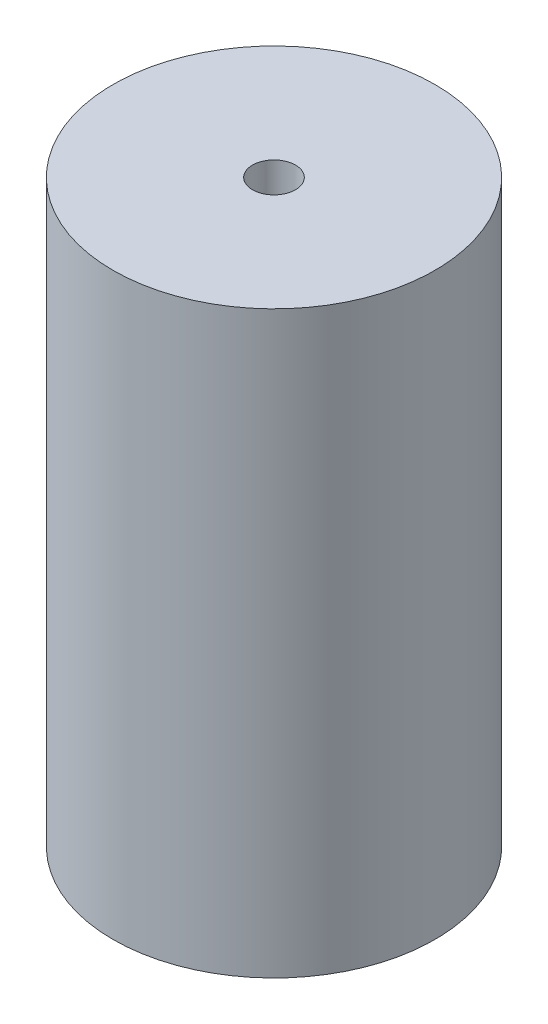
SolidWorks part; units mm, degrees
ref_plane "Front Plane" through (0, 0, 0) normal (0, 0, 1) x (1, 0, 0)
ref_plane "Top Plane" through (0, 0, 0) normal (0, 1, 0) x (1, 0, 0)
ref_plane "Right Plane" through (0, 0, 0) normal (1, 0, 0) x (0, 0, -1)
sketch "Sketch1" plane through (0, 0, 0) normal (0, 1, 0) x (1, 0, 0)
  circle A0 centre (0, 0) radius 7.5
  dimension "D1" = 15
extrude "Boss-Extrude1" add sketch "Sketch1" along normal blind 27
sketch "Sketch2" plane through (0, 0, 0) normal (0, -1, 0) x (1, 0, 0)
  circle A0 centre (0, 0) radius 5
  dimension "D1" = 10
extrude "Cut-Extrude1" cut sketch "Sketch2" against normal blind 11
sketch "Sketch3" plane through (0, 27, 0) normal (0, 1, 0) x (1, 0, 0)
  circle A0 centre (0, 0) radius 1
  dimension "D1" = 2
extrude "Cut-Extrude2" cut sketch "Sketch3" against normal blind 11
sketch "Sketch4" plane through (0, 0, 0) normal (0, 0, 1) x (1, 0, 0)
  line L0 (-7.5, 0) -> (7.5, 0) construction
  line L1 (7.5, 27) -> (-7.5, 27) construction
  circle A0 centre (0, 22) radius 1.6
  circle A1 centre (0, 5) radius 1.6
  dimension "D1" = 3.2
  dimension "D2" = 3.2
  dimension "D3" = 5
  dimension "D4" = 5
extrude "Cut-Extrude3" cut sketch "Sketch4" against normal blind 11
chamfer "Chamfer1" distance 1 angle 60 1 edges at (0, 0, -5)
